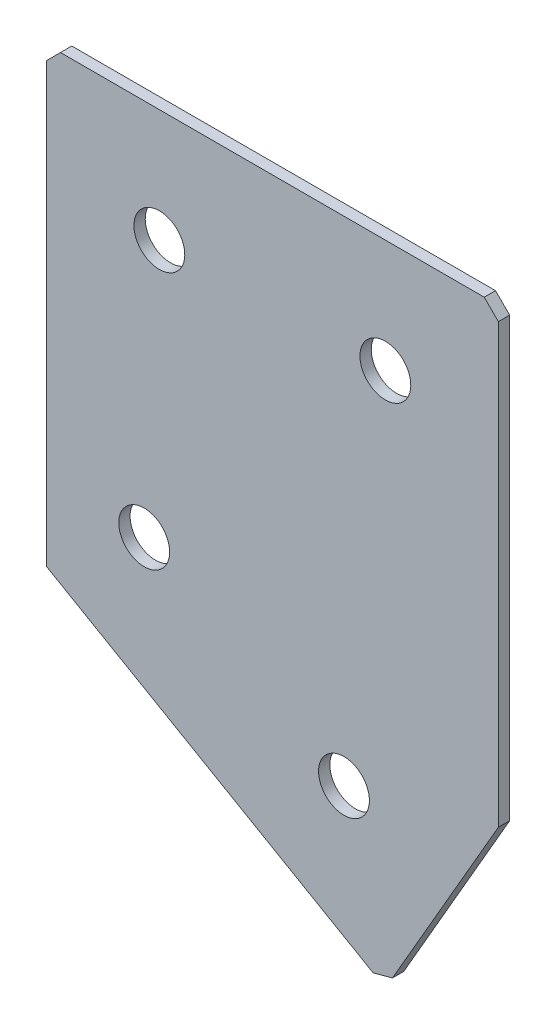
SolidWorks part; units mm, degrees
material "Простая углеродистая сталь"
ref_plane "Спереди" through (0, 0, 0) normal (0, 0, 1) x (1, 0, 0)
ref_plane "Сверху" through (0, 0, 0) normal (0, 1, 0) x (1, 0, 0)
ref_plane "Справа" through (0, 0, 0) normal (1, 0, 0) x (0, 0, -1)
sketch "Эскиз3" plane through (0, 0, 0) normal (0, 0, -1) x (1, 0, 0)
  line L0 (0, 0) -> (80, 0)
  line L1 (80, 0) -> (80, 80)
  line L2 (0, 0) -> (0, 80)
  line L3 (0, 80) -> (60, 114.641)
  line L4 (60, 114.641) -> (80, 80)
  dimension "D1" = 80
  dimension "D2" = 80
  dimension "D3" = 40
  dimension "D4" = 30
  dimension "D5" = 80
extrude "Бобышка-Вытянуть1" add sketch "Эскиз3" along normal blind 2
hole_wizard "Отверстие с зазором M81" positions "Эскиз4" profile "Эскиз5" hole size "M8" standard "DIN" end condition through all
sketch "Эскиз4" plane through (0, 0, -2) normal (0, 0, -1) x (1, 0, 0)
  line L0 (17.3205, 66.906) -> (52.6795, 87.3205) construction
  line L2 (60, 114.641) -> (0, 80) construction
  line L3 (20, 20) -> (60, 20) construction
  line L5 (0, 0) -> (80, 0) construction
  line L6 (0, 80) -> (0, 0) construction
  line L7 (80, 0) -> (80, 80) construction
  line L8 (80, 80) -> (60, 114.641) construction
  line L9 (17.3205, 66.906) -> (0, 56.906) construction
  point P0 (20, 20)
  point P2 (60, 20)
  point P4 (17.3205, 66.906)
  point P6 (52.6795, 87.3205)
  dimension "D1" = 20
  dimension "D2" = 20
  dimension "D3" = 20
  dimension "D4" = 20
  dimension "D5" = 20
  dimension "D6" = 20
  dimension "D7" = 40.829
  dimension "D8" = 40
sketch "Эскиз5" plane through (20, -20, -2) normal (1, 0, 0) x (0, 1, 0)
  line L0 (0, 0) -> (0, 2)
  line L1 (0, 2) -> (4.5, 2)
  line L2 (4.5, 2) -> (4.5, 0)
  line L5 (4.5, 0) -> (0, 0)
  line L11 (0, -6.35) -> (0, 107.95) construction
  dimension "Диаметр сквозного отверстия" = 9
  dimension "Глубина сквозного отверстия" = 2
chamfer "Фаска1" distance 2.5 distance2 2.5 3 edges at (60, -114.641, -1) (80, 0, -1) (0, 0, -1)
